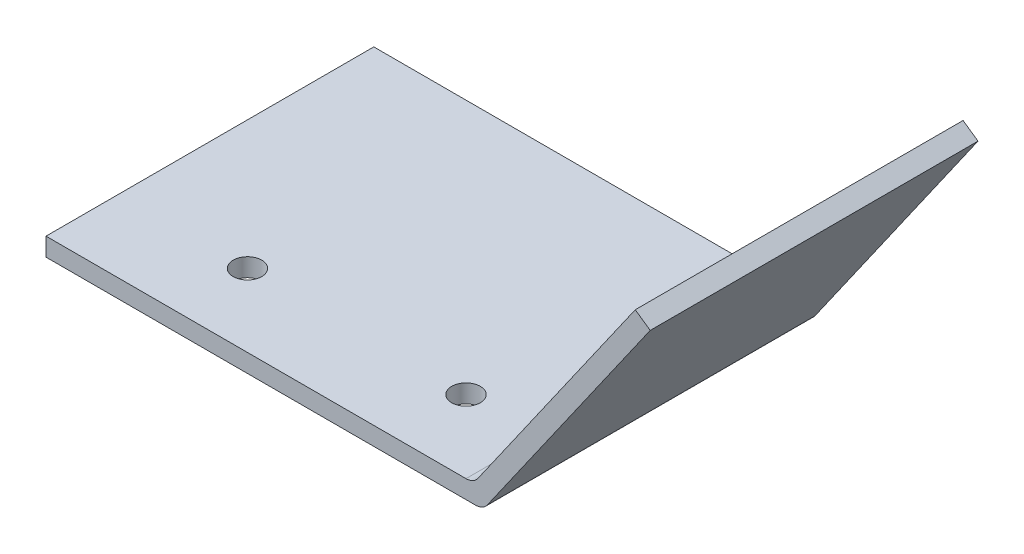
SolidWorks part; units mm, degrees
ref_plane "Front Plane" through (0, 0, 0) normal (0, 0, 1) x (1, 0, 0)
ref_plane "Top Plane" through (0, 0, 0) normal (0, 1, 0) x (1, 0, 0)
ref_plane "Right Plane" through (0, 0, 0) normal (1, 0, 0) x (0, 0, -1)
sketch "Sketch1" plane through (0, 0, 0) normal (0, 0, 1) x (1, 0, 0)
  line L0 (73.5992, 1.8211) -> (76.2, 0)
  line L1 (0, 0) -> (76.2, 0)
  line L2 (0, 0) -> (0, 3.175)
  line L3 (0, 3.175) -> (76.2, 3.175)
  line L4 (76.2, 0) -> (76.2, 3.175)
  line L5 (73.5992, 1.8211) -> (102.7369, 43.434)
  line L6 (76.2, 0) -> (105.3377, 41.6129)
  line L7 (102.7369, 43.434) -> (105.3377, 41.6129)
  dimension "D1" = 3.175
  dimension "D2" = 76.2
  dimension "D3" = 50.8
  dimension "D4" = 125
extrude "Boss-Extrude1" add sketch "Sketch1" along normal mid plane 57.15 contours L0 L5 L3 L2 L1 | L7 L5 L3 L4 L6 | L5 L0 L4 L3
fillet "Fillet1" radius 2.54 1 edges at (74.5472, 3.175, 0)
fillet "Fillet2" radius 2.54 1 edges at (76.2, 0, 0)
sketch "Sketch2" plane through (0, 3.175, 0) normal (0, 1, 0) x (1, 0, 0)
  line L0 (73.225, -15.875) -> (0, -15.875) construction
  line L1 (73.225, -28.575) -> (73.225, 28.575) construction
  line L2 (0, -28.575) -> (0, 28.575) construction
  line L3 (0, -28.575) -> (73.225, -28.575) construction
  circle A0 centre (60.525, -15.875) radius 2.4892
  circle A1 centre (22.425, -15.875) radius 2.4892
  dimension "D2" = 4.9784
  dimension "D3" = 4.9784
  dimension "D1" = 12.7
  dimension "D4" = 12.7
  dimension "D5" = 38.1
extrude "Cut-Extrude1" cut sketch "Sketch2" against normal through all
